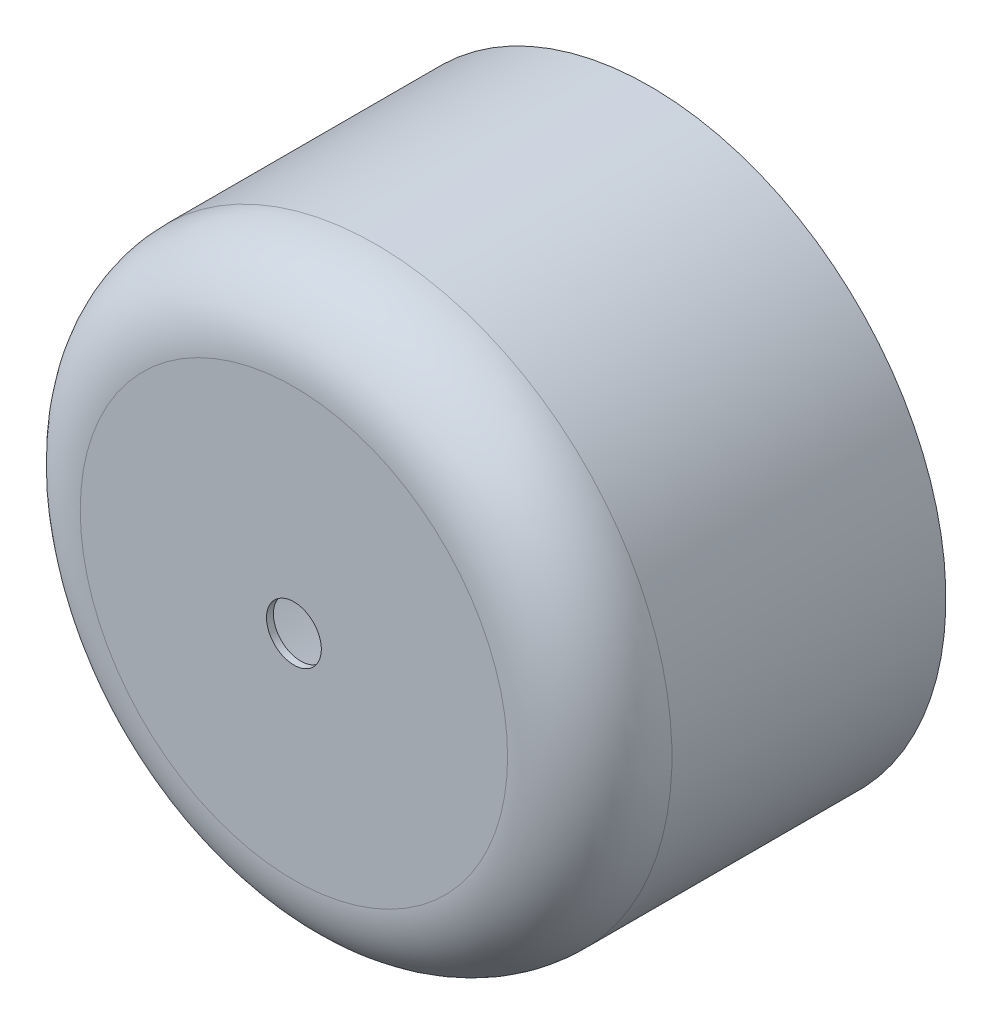
SolidWorks part; units mm, degrees
ref_plane "Piano frontale" through (0, 0, 0) normal (0, 0, 1) x (1, 0, 0)
ref_plane "Piano superiore" through (0, 0, 0) normal (0, 1, 0) x (1, 0, 0)
ref_plane "Piano destro" through (0, 0, 0) normal (1, 0, 0) x (0, 0, -1)
ref_plane "Piano1" through (0, 0, 0) normal (0, -1, 0) x (1, 0, 0)
sketch "Schizzo1" plane through (0, 0, 0) normal (0, -1, 0) x (1, 0, 0)
  line L0 (10.8, 0) -> (10.8, 10)
  line L1 (7.8, 13) -> (1, 13)
  line L2 (1, 13) -> (1, 12.75)
  line L3 (1, 12.75) -> (7.8, 12.75)
  line L4 (10.55, 10) -> (10.55, 0)
  line L5 (10.55, 0) -> (10.8, 0)
  line L6 (0, 13) -> (0, 0) construction
  arc A0 (10.8, 10) -> (7.8, 13) centre (7.8, 10) ccw
  arc A1 (7.8, 12.75) -> (10.55, 10) centre (7.8, 10) cw
revolve "Rivoluzione1" add sketch "Schizzo1" angle 360 about L6
